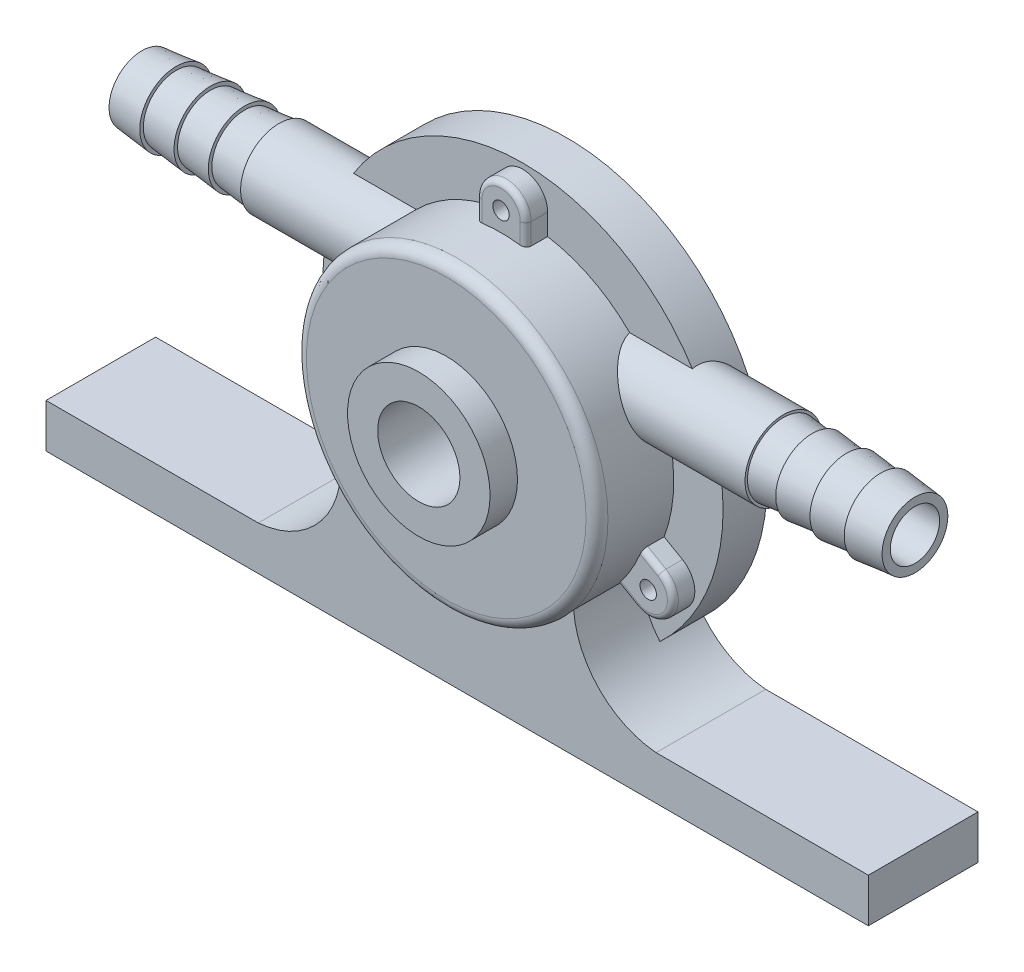
SolidWorks part; units mm, degrees
ref_plane "Front Plane" through (0, 0, 0) normal (0, 0, 1) x (1, 0, 0)
ref_plane "Top Plane" through (0, 0, 0) normal (0, 1, 0) x (1, 0, 0)
ref_plane "Right Plane" through (0, 0, 0) normal (1, 0, 0) x (0, 0, -1)
sketch "Sketch1" plane through (0, 0, 0) normal (0, 0, 1) x (1, 0, 0)
  circle A0 centre (0, 0) radius 36.5
  dimension "D1" = 73
extrude "Boss-Extrude1" add sketch "Sketch1" along normal blind 8
sketch "Sketch2" plane through (0, 0, 8) normal (0, 0, 1) x (1, 0, 0)
  circle A0 centre (0, 0) radius 27.5
  dimension "D1" = 55
extrude "Boss-Extrude2" add sketch "Sketch2" along normal blind 14
sketch "Sketch3" plane through (0, 0, 22) normal (0, 0, 1) x (1, 0, 0)
  circle A0 centre (0, 0) radius 13
  dimension "D1" = 26
extrude "Boss-Extrude3" add sketch "Sketch3" along normal blind 5
sketch "Sketch4" plane through (0, 0, 27) normal (0, 0, 1) x (1, 0, 0)
  circle A0 centre (0, 0) radius 7.5
  dimension "D1" = 15
extrude "Cut-Extrude1" cut sketch "Sketch4" against normal blind 14
ref_plane "Plane2" through (36.5, 0, 0) normal (1, 0, 0) x (0, 0, -1)
sketch "Sketch6" plane through (36.5, 0, 0) normal (1, 0, 0) x (0, 0, -1)
  line L0 (0, -36.5) -> (0, 36.5) construction
  line L2 (-8, 27.5) -> (-22, 27.5) construction
  circle A0 centre (-7, 12.5) radius 7
  dimension "D1" = 14
  dimension "D2" = 7
  dimension "D3" = 15
extrude "Boss-Extrude4" add sketch "Sketch6" along normal blind 10 and the other way blind 82
sketch "Sketch8" plane through (0, 0, 0) normal (0, 0, -1) x (-1, 0, 0)
  circle A1 centre (0, 0) radius 7.5 construction
  arc A3 (-17.6535, 13.95) -> (17.6535, 13.95) centre (0, 0) ccw
  arc A4 (-17.6535, 13.95) -> (17.6535, 13.95) centre (0, -22.5) cw
  point P2 (0, -7.5)
  dimension "D1" = 45
  dimension "D2" = 40.5
extrude "Cut-Extrude2" cut sketch "Sketch8" against normal blind 12
sketch "Sketch10" plane through (46.5, 0, 0) normal (1, 0, 0) x (0, 0, -1)
  circle A0 centre (-7, 12.5) radius 4.5
  dimension "D1" = 9
sketch "Sketch11" plane through (0, 0, 0) normal (0, 0, -1) x (-1, 0, 0)
  circle A0 centre (0, 31) radius 1.5
  circle A1 centre (0, 0) radius 36.5 construction
  circle A7 centre (26.8468, -15.5) radius 1.5
  circle A8 centre (-26.8468, -15.5) radius 1.5
  arc A9 (34.2929, 12.5) -> (-34.2929, 12.5) centre (0, 0) ccw construction
  point P13 (0, -1)
  point P14 (0, 0)
  point P15 (0, -1)
  dimension "D1" = 3
  dimension "D3" = 3
  dimension "D4" = 26.8468
  dimension "D5" = 31
  dimension "D2" = 31
extrude "Cut-Extrude4" cut sketch "Sketch11" against normal through all
fillet "Fillet1" radius 2 1 edges at (27.5, 0, 22)
extrude "Cut-Extrude5" cut sketch "Sketch10" against normal through all
sketch "Sketch12" plane through (0, 0, 13) normal (0, 0, 1) x (1, 0, 0)
  circle A0 centre (0, 0) radius 3.2
  dimension "D1" = 6.4
extrude "Cut-Extrude6" cut sketch "Sketch12" against normal through all
sketch "Sketch13" plane through (0, 0, 0) normal (0, 0, -1) x (-1, 0, 0)
  circle A0 centre (0, 0) radius 25
  circle A1 centre (0, 0) radius 27.3
extrude "Cut-Extrude7" cut sketch "Sketch13" against normal blind 1.2
sketch "Sketch14" plane through (0, 0, 8) normal (0, 0, 1) x (1, 0, 0)
  line L0 (4.5, 31) -> (4.5, 27.1293)
  line L1 (-4.5, 31) -> (-4.5, 27.1293)
  line L2 (29.0968, -11.6029) -> (25.7447, -9.6675)
  line L3 (24.5968, -19.3971) -> (21.2447, -17.4618)
  line L4 (-24.5968, -19.3971) -> (-21.2447, -17.4618)
  line L5 (-29.0968, -11.6029) -> (-25.7447, -9.6675)
  arc A2 (4.5, 31) -> (-4.5, 31) centre (0, 31) ccw
  arc A3 (19.4627, 19.4282) -> (-19.4627, 19.4282) centre (0, 0) ccw construction
  arc A4 (24.5968, -19.3971) -> (29.0968, -11.6029) centre (26.8468, -15.5) ccw
  arc A5 (-29.0968, -11.6029) -> (-24.5968, -19.3971) centre (-26.8468, -15.5) ccw
  arc A6 (21.2447, -17.4618) -> (25.7447, -9.6675) centre (0, 0) ccw
  arc A7 (-25.7447, -9.6675) -> (-21.2447, -17.4618) centre (0, 0) ccw
  arc A8 (4.5, 27.1293) -> (-4.5, 27.1293) centre (0, 0) ccw
  point P27 (0, 0)
  dimension "D1" = 9
  dimension "D2" = 3
extrude "Boss-Extrude5" add sketch "Sketch14" along normal blind 4
fillet "Fillet2" radius 1 9 edges at (4.5, 29.0647, 12) (-4.5, 29.0647, 12) (22.9207, -18.4294, 12) (27.4207, -10.6352, 12) (-27.4207, -10.6352, 12) (-22.9207, -18.4294, 12) (0, 35.5, 12) (30.7439, -17.75, 12) (-30.7439, -17.75, 12)
sketch "Sketch15" plane through (0, 0, 0) normal (0, 0, -1) x (-1, 0, 0)
  circle A0 centre (0, 31) radius 1.5
  circle A1 centre (26.8468, -15.5) radius 1.5
  circle A2 centre (-26.8468, -15.5) radius 1.5
  point P10 (0, 0)
  dimension "D1" = 3
  dimension "D4" = 26.8468
  dimension "D3" = 15.5
  dimension "D2" = 3
extrude "Cut-Extrude8" cut sketch "Sketch15" against normal through all
ref_plane "Plane3" through (0, 12.5, 0) normal (0, 1, 0) x (1, 0, 0)
sketch "Sketch16" plane through (0, 12.5, 0) normal (0, 1, 0) x (1, 0, 0)
  line L0 (-70.5, -13) -> (-64.25, -13.65)
  line L3 (-45.5, 0) -> (-45.5, -14) construction
  line L4 (-70.5, -1) -> (-45.5, -1) construction
  line L5 (0, 0) -> (0, -60.1535) construction
  line L6 (70.5, -13) -> (70.5, -7)
  line L7 (-64.25, -13.65) -> (-64.25, -13)
  line L8 (-64.25, -13) -> (-58, -13.65)
  line L9 (-58, -13.65) -> (-58, -13)
  line L10 (-58, -13) -> (-51.75, -13.65)
  line L11 (-51.75, -13.65) -> (-51.75, -13)
  line L12 (-51.75, -13) -> (-45.5, -13.65)
  line L13 (-45.5, -13.65) -> (-45.5, -13)
  line L14 (70.5, -7) -> (45.5, -7)
  line L15 (-70.5, -7) -> (-45.5, -7)
  line L16 (-70.5, -13) -> (-70.5, -7)
  line L17 (-45.5, -7) -> (-45.5, -13)
  line L18 (45.5, -7) -> (45.5, -13)
  line L19 (45.5, -13.65) -> (45.5, -13)
  line L20 (51.75, -13) -> (45.5, -13.65)
  line L21 (51.75, -13.65) -> (51.75, -13)
  line L22 (58, -13) -> (51.75, -13.65)
  line L23 (58, -13.65) -> (58, -13)
  line L24 (64.25, -13) -> (58, -13.65)
  line L25 (64.25, -13.65) -> (64.25, -13)
  line L26 (70.5, -13) -> (64.25, -13.65)
  point P0 (-45.5, -7)
  line B0 (-70.5, -13) -> (-70.5, -1) construction
  line B1 (-70.5, -13) -> (-45.5, -13) construction
  line B2 (-45.5, -13) -> (-45.5, -1) construction
  line B3 (-70.5, -13) -> (-45.5, -1) construction
  line B4 (-45.5, -13) -> (-70.5, -1) construction
  line B5 (-68.289, -13.65) -> (-41.9667, -13.65) construction
  line B6 (-58, -7) -> (-26.614, -7) construction
  line B7 (-70.5, -12.2) -> (-45.5, -12.2)
sketch_block_instance "Block1-1"
sketch_block "Block1" parameters "D1"=12, "D2"=25, "D3"=0.65, "D4"=0.8
revolve "Revolve1" add sketch "Sketch16" angle 360 about L14
sketch "Sketch17" plane through (70.5, 0, 0) normal (1, 0, 0) x (0, 0, -1)
  circle A0 centre (-7, 12.5) radius 4.5
  dimension "D1" = 9
extrude "Cut-Extrude9" cut sketch "Sketch17" against normal through all
ref_plane "Plane4" through (0, 0, 4) normal (0, 0, -1) x (-1, 0, 0)
sketch "Sketch18" plane through (0, 0, 4) normal (0, 0, -1) x (-1, 0, 0)
  line L1 (-75, -32.5) -> (-36.2829, -32.5)
  line L2 (-75, -32.5) -> (-75, -40.5)
  line L3 (-75, -40.5) -> (75, -40.5)
  line L4 (75, -32.5) -> (75, -40.5)
  line L5 (-75, -32.5) -> (75, -40.5) construction
  line L6 (-75, -40.5) -> (75, -32.5) construction
  line L8 (36.2829, -32.5) -> (75, -32.5)
  line L9 (0, 0) -> (0, 59.8133) construction
  arc A0 (-34.2929, 12.5) -> (34.2929, 12.5) centre (0, 0) ccw construction
  arc A7 (-21.2447, -17.4618) -> (21.2447, -17.4618) centre (0, 0) ccw
  arc A8 (36.2829, -32.5) -> (21.2447, -17.4618) centre (37.5945, -16.1502) cw
  arc A9 (-36.2829, -32.5) -> (-21.2447, -17.4618) centre (-37.5945, -16.1502) ccw
  point P0 (0, -36.5)
  point P17 (25, -32.5)
  dimension "D3" = 150
  dimension "D4" = 8
extrude "Boss-Extrude7" add sketch "Sketch18" against normal blind 16 and the other way blind 4
